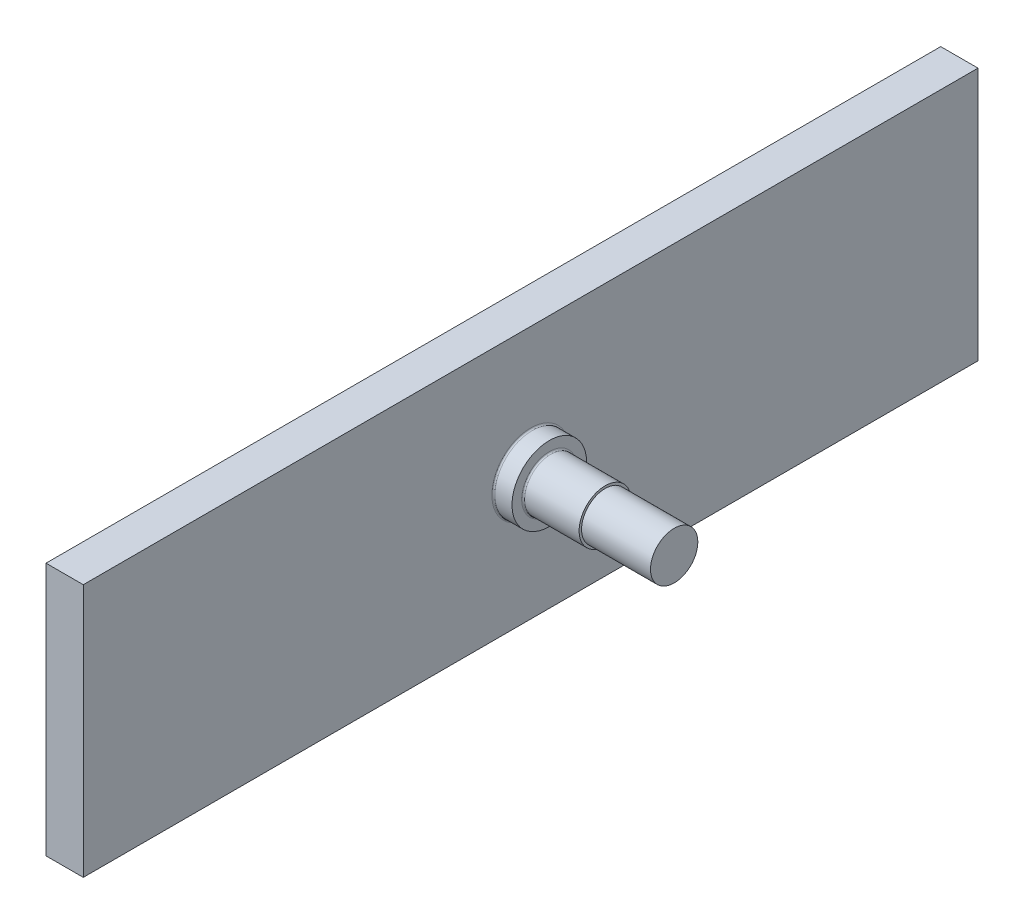
SolidWorks part; units mm, degrees
material "1060 Alloy"
ref_plane "Front" through (0, 0, 0) normal (0, 0, 1) x (1, 0, 0)
ref_plane "Top" through (0, 0, 0) normal (0, 1, 0) x (1, 0, 0)
ref_plane "Right" through (0, 0, 0) normal (1, 0, 0) x (0, 0, -1)
sketch "Sketch1" plane through (0, 0, 0) normal (1, 0, 0) x (0, 0, -1)
  line L1 (0, 0) -> (-120, 0)
  line L2 (0, 0) -> (0, 34)
  line L3 (0, 34) -> (-120, 34)
  line L4 (-120, 0) -> (-120, 34)
  dimension "D1" = 34
  dimension "D2" = 120
extrude "Boss-Extrude1" add sketch "Sketch1" along normal blind 5
sketch "Sketch2" plane through (5, 0, 0) normal (1, 0, 0) x (0, 0, -1)
  line L0 (-60, 34) -> (-60, 0)
  line L1 (0, 34) -> (-120, 34) construction
  line L2 (0, 0) -> (-120, 0) construction
  circle A0 centre (-60, 17) radius 5
  dimension "D1" = 10
extrude "Boss-Extrude2" add sketch "Sketch2" along normal blind 2.5 contours L0 A0 | L0 A0
sketch "Sketch3" plane through (7.5, 0, 0) normal (1, 0, 0) x (0, 0, -1)
  circle A0 centre (-60, 17) radius 3.5
  dimension "D1" = 7
extrude "Boss-Extrude3" add sketch "Sketch3" along normal blind 16.75
sketch "Sketch4" plane through (24.25, 0, 0) normal (1, 0, 0) x (0, 0, -1)
  circle A0 centre (-60, 17) radius 3.5
  circle A1 centre (-60, 17) radius 3.175
  dimension "D1" = 6.35
extrude "Cut-Extrude1" cut sketch "Sketch4" against normal offset from surface (9.25 mm away) 7.5 up to face at (7.5, 17, 56.5)
fillet "Fillet1" radius 0.2 2 edges at (7.5, 17, 56.5) (5, 17, 55)
